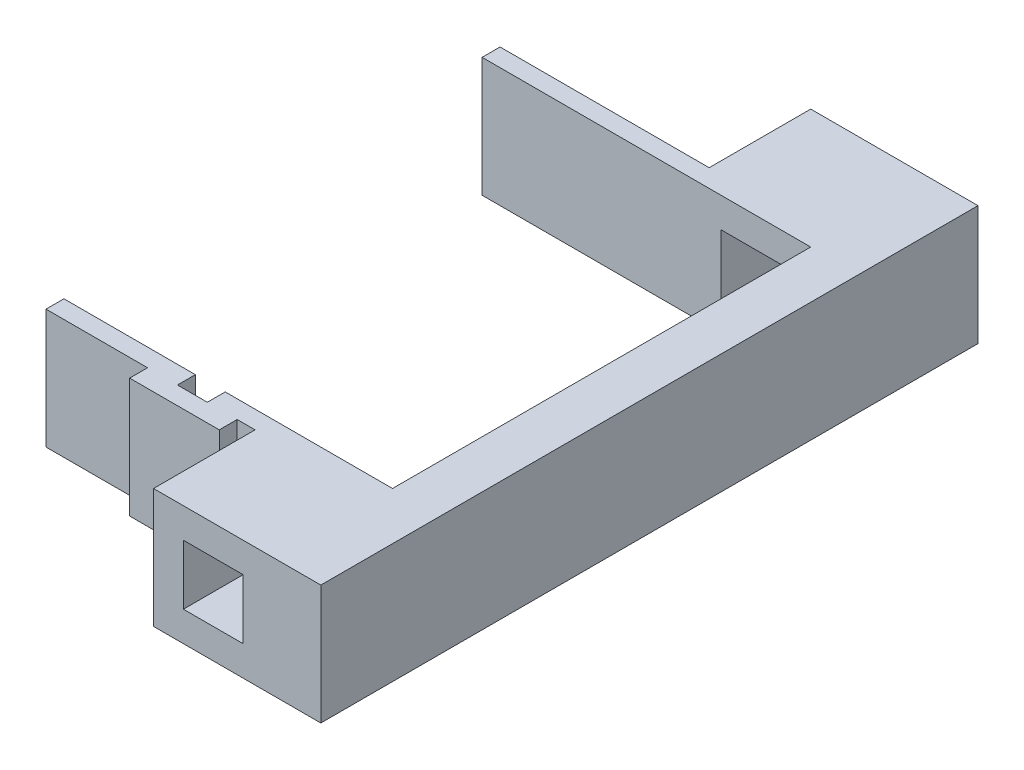
SolidWorks part; units mm, degrees
ref_plane "Front Plane" through (0, 0, 0) normal (0, 0, 1) x (1, 0, 0)
ref_plane "Top Plane" through (0, 0, 0) normal (0, 1, 0) x (1, 0, 0)
ref_plane "Right Plane" through (0, 0, 0) normal (1, 0, 0) x (0, 0, -1)
sketch "Sketch1" plane through (0, 0, 0) normal (0, 1, 0) x (1, 0, 0)
  line L0 (0, 0) -> (406.7942, 0) construction
  line L5 (0, 0) -> (0, -234.8819) construction
  line L6 (10, -35) -> (10, -55)
  line L11 (-10, 35) -> (10, 35)
  line L12 (-10, 35) -> (-10, 55)
  line L16 (-10, 55) -> (10, 55)
  line L17 (10, 35) -> (10, 55)
  line L19 (-10, -55) -> (10, -55)
  line L22 (-10, -35) -> (-10, -55)
  line L26 (-10, -35) -> (10, -35)
  line L37 (10, 55) -> (18, 55)
  line L38 (10, 55) -> (10, -55)
  line L39 (10, -55) -> (18, -55)
  line L40 (18, 55) -> (18, -55)
  dimension "D1" = 35
  dimension "D2" = 20
  dimension "D3" = 20
  dimension "D4" = 8
extrude "Boss-Extrude1" add sketch "Sketch1" along normal mid plane 20 contours L40 L37 L17 L38 L6 L39 | L26 L22 L19 L6 | L11 L17 L16 L12
sketch "Sketch3" plane through (0, 0, 55) normal (0, 0, 1) x (1, 0, 0)
  line L1 (5, -5) -> (-5, -5)
  line L2 (5, -5) -> (5, 5)
  line L3 (5, 5) -> (-5, 5)
  line L4 (-5, -5) -> (-5, 5)
  line L5 (5, -5) -> (-5, 5) construction
  line L6 (5, 5) -> (-5, -5) construction
  point P0 (0, 0)
  dimension "D1" = 10
  dimension "D2" = 10
extrude "Cut-Extrude1" cut sketch "Sketch3" against normal through all
sketch "Sketch4" plane through (0, 0, 0) normal (0, 1, 0) x (1, 0, 0)
  line L1 (-10, -35) -> (-18, -35)
  line L2 (-10, -35) -> (-10, -38)
  line L3 (-10, -38) -> (-13, -38)
  line L4 (-18, -35) -> (-18, -38)
  line L5 (-10, 35) -> (-45, 35)
  line L6 (-10, 35) -> (-10, 38)
  line L7 (-10, 38) -> (-45, 38)
  line L8 (-45, 35) -> (-45, 38)
  line L9 (-23, -35) -> (-45, -35)
  line L10 (-23, -35) -> (-23, -38)
  line L11 (-28, -38) -> (-45, -38)
  line L12 (-45, -35) -> (-45, -38)
  line L13 (-23, -38) -> (-18, -38)
  line L14 (-28, -38) -> (-28, -41)
  line L15 (-28, -41) -> (-13, -41)
  line L16 (-13, -38) -> (-13, -41)
  dimension "D1" = 3
  dimension "D2" = 3
  dimension "D3" = 8
  dimension "D4" = 5
  dimension "D5" = 3
  dimension "D6" = 22
  dimension "D7" = 5
  dimension "D8" = 5
extrude "Boss-Extrude2" add sketch "Sketch4" along normal mid plane 20 contours L16 L3 L13 L11 L14 L15 | L1 L4 L3 L2 | L7 L8 L5 L6
